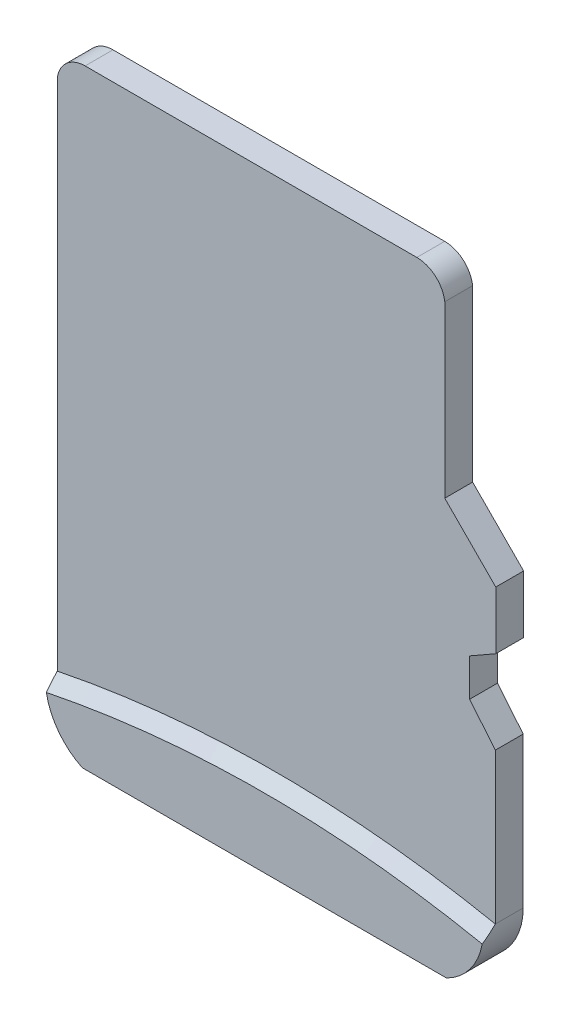
SolidWorks part; units mm, degrees
other "Camera1"
ref_plane "Front Plane" through (0, 0, 0) normal (0, 0, 1) x (1, 0, 0)
ref_plane "Top Plane" through (0, 0, 0) normal (0, 1, 0) x (1, 0, 0)
ref_plane "Right Plane" through (0, 0, 0) normal (1, 0, 0) x (0, 0, -1)
sketch "Sketch1" plane through (0, 0, 0) normal (0, 0, 1) x (1, 0, 0)
  line L0 (19.1531, 24.0335) -> (27.4834, 24.0335)
  line L1 (28.1851, 23.4204) -> (28.1851, 19.1475)
  line L2 (28.1851, 19.1475) -> (29.466, 17.856)
  line L3 (29.466, 17.856) -> (29.466, 16.4054)
  line L4 (28.8097, 16.0308) -> (28.8097, 15.0873)
  line L5 (28.8097, 15.0873) -> (29.4551, 14.3035)
  line L6 (29.4551, 14.3035) -> (29.4551, 10.5216)
  line L7 (28.8097, 16.0308) -> (29.466, 16.4054)
  line L8 (18.4539, 23.4204) -> (18.4539, 10.5216)
  line L9 (19.3821, 9.0335) -> (28.5269, 9.0335)
  arc A0 (28.1851, 23.4204) -> (27.4834, 24.0335) centre (27.486, 23.3283) ccw
  arc A1 (18.4539, 10.5216) -> (19.3821, 9.0335) centre (20.0948, 10.5115) ccw
  arc A2 (29.4551, 10.5216) -> (18.4539, 10.5216) centre (23.9545, -16.6696) ccw
  arc A3 (28.5269, 9.0335) -> (29.4551, 10.5216) centre (27.7888, 10.5274) ccw
  arc A4 (19.1556, 24.0335) -> (18.4539, 23.4204) centre (19.1531, 23.3283) ccw
sketch "Sketch2" plane through (0, 0, 0) normal (0, 0, 1) x (1, 0, 0)
  line L0 (19.3821, 9.0335) -> (28.5269, 9.0335)
  arc A0 (18.4539, 10.5216) -> (29.4551, 10.5216) centre (23.9545, -16.6696) cw
  arc A1 (29.4551, 10.5216) -> (28.5269, 9.0335) centre (27.7888, 10.5274) cw
  arc A2 (19.3821, 9.0335) -> (18.4539, 10.5216) centre (20.0948, 10.5115) cw
extrude "Extrude1" add sketch "Sketch1" along normal blind 0.7 contours L0 A4 L8 A2 L6 L5 L4 L7 L3 L2 L1 A0 | L9 A3 A2 A1
extrude "Extrude2" add sketch "Sketch2" along normal blind 1
draft "Draft1" type of draft neutral plane draft angle 45 faces to draft 1 face at (23.9545, 10.797, 0.85) neutral plane through (23.9599, 1.9183, 0.7) neutral plane normal (0, 0, 1) parameters "D1"=45
